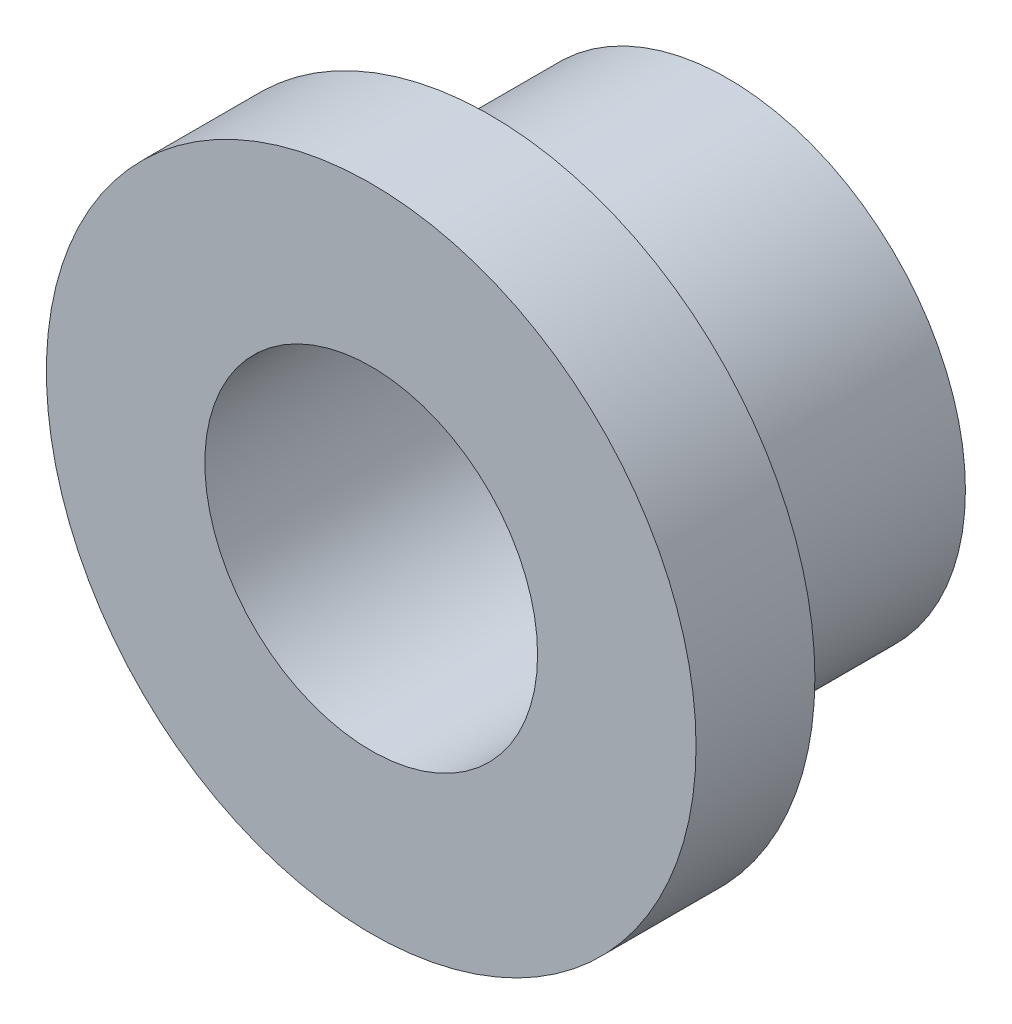
SolidWorks part; units mm, degrees
material "Nylon 6/10"
ref_plane "Front Plane" through (0, 0, 0) normal (0, 0, 1) x (1, 0, 0)
ref_plane "Top Plane" through (0, 0, 0) normal (0, 1, 0) x (1, 0, 0)
ref_plane "Right Plane" through (0, 0, 0) normal (1, 0, 0) x (0, 0, -1)
sketch "Sketch1" plane through (0, 0, 0) normal (1, 0, 0) x (0, 0, -1)
  line L0 (0, 2.1) -> (0, 4.1)
  line L1 (0, 4.1) -> (1.5, 4.1)
  line L2 (1.5, 4.1) -> (1.5, 3)
  line L3 (1.5, 3) -> (4.5, 3)
  line L4 (4.5, 3) -> (4.5, 2.1)
  line L5 (4.5, 2.1) -> (0, 2.1)
  line L6 (-8.0305, 0) -> (18.6209, 0) construction
  dimension "D1" = 4.2
  dimension "D2" = 8.2
  dimension "D3" = 6
  dimension "D4" = 1.5
  dimension "D5" = 3
revolve "Revolve1" add sketch "Sketch1" angle 360 about L6
